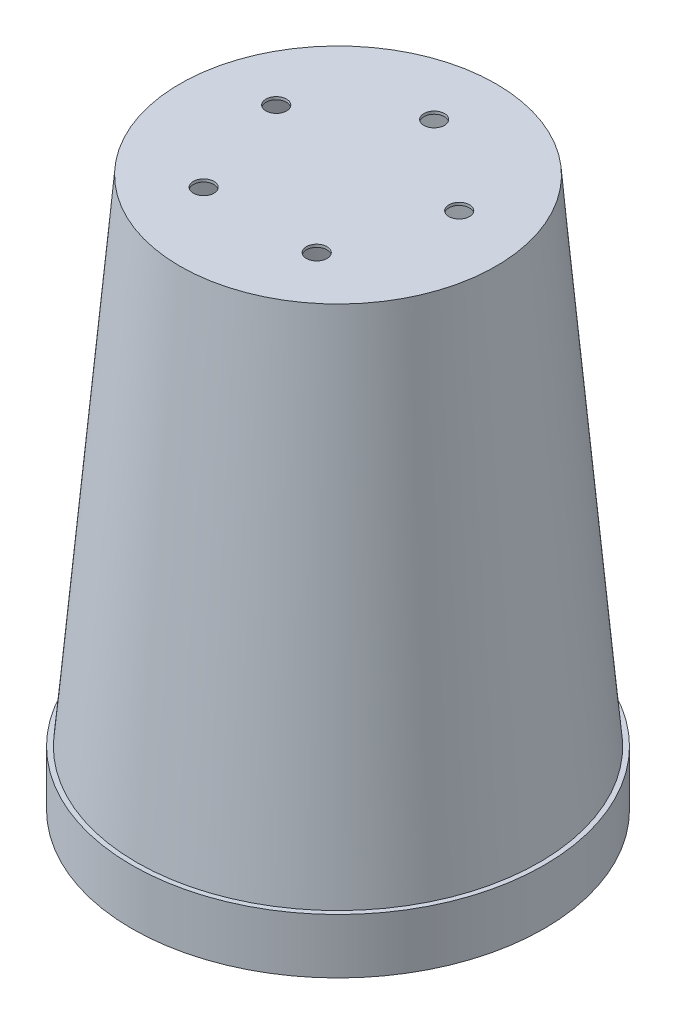
SolidWorks part; units mm, degrees
ref_plane "Front Plane" through (0, 0, 0) normal (0, 0, 1) x (1, 0, 0)
ref_plane "Top Plane" through (0, 0, 0) normal (0, 1, 0) x (1, 0, 0)
ref_plane "Right Plane" through (0, 0, 0) normal (1, 0, 0) x (0, 0, -1)
sketch "Sketch1" plane through (0, 0, 0) normal (0, 1, 0) x (1, 0, 0)
  circle A0 centre (0, 0) radius 75
  dimension "D1" = 150
extrude "Boss-Extrude1" add sketch "Sketch1" along normal blind 200 draft 5
sketch "Sketch2" plane through (0, 0, 0) normal (0, 1, 0) x (1, 0, 0)
  circle A0 centre (0, 0) radius 75
extrude "Boss-Extrude2" add sketch "Sketch2" along normal blind 20
shell "Shell2" thickness 1
sketch "Sketch3" plane through (0, 200, 0) normal (0, 1, 0) x (1, 0, 0)
  circle A0 centre (0, 35) radius 3.75
  point P2 (0, 0)
  dimension "D1" = 7.5
  dimension "D2" = 35
extrude "Cut-Extrude1" cut sketch "Sketch3" against normal up to next
pattern_circular "CirPattern1" count 5 over 360 about axis through (0, 0, 0) along (0, 1, 0) of "Cut-Extrude1"
